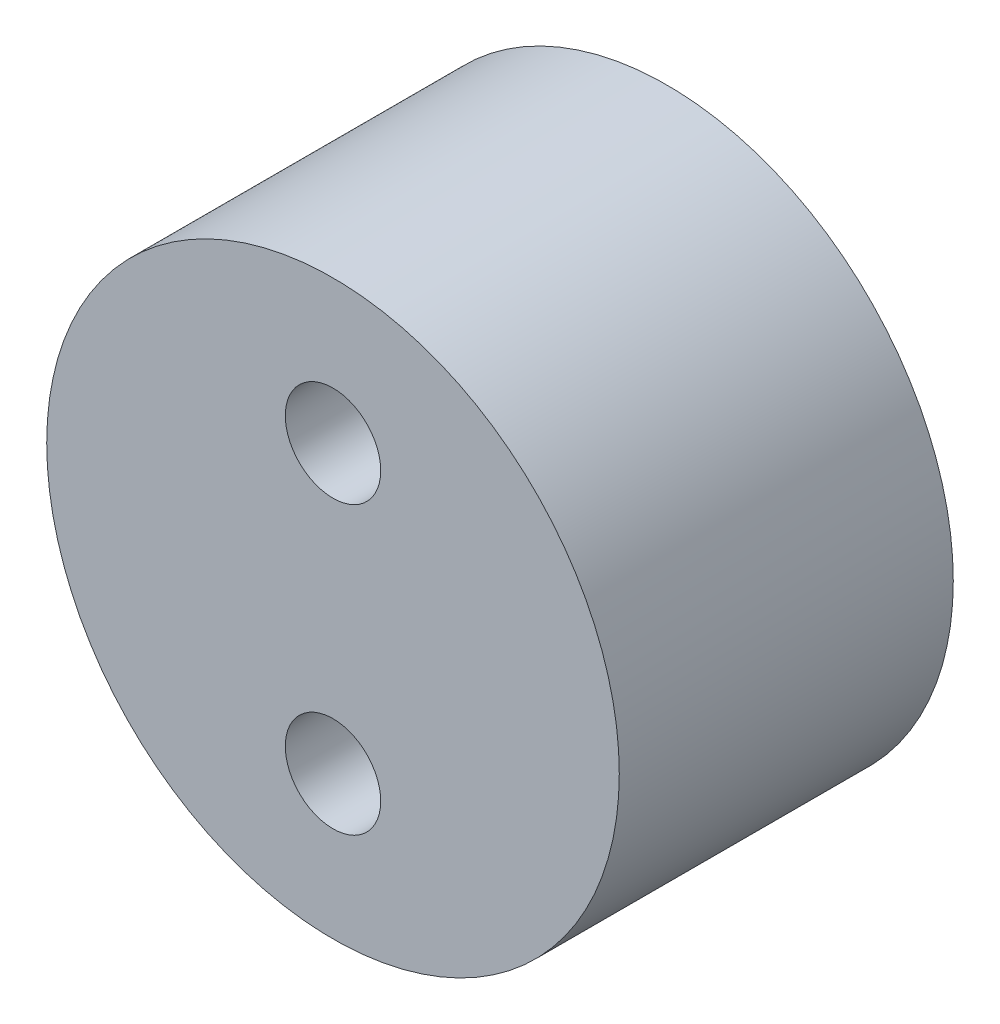
SolidWorks part; units mm, degrees
ref_plane "Front Plane" through (0, 0, 0) normal (0, 0, 1) x (1, 0, 0)
ref_plane "Top Plane" through (0, 0, 0) normal (0, 1, 0) x (1, 0, 0)
ref_plane "Right Plane" through (0, 0, 0) normal (1, 0, 0) x (0, 0, -1)
sketch "Sketch1" plane through (0, 0, 0) normal (0, 0, 1) x (1, 0, 0)
  line L0 (0, -7.5) -> (0, 7.5) construction
  circle A0 centre (0, 0) radius 15
  circle A1 centre (0, 7.5) radius 2.5
  circle A2 centre (0, -7.5) radius 2.5
  point P6 (0, 0)
  dimension "D2" = 30
  dimension "D3" = 5
  dimension "D4" = 5
  dimension "D1" = 15
extrude "Boss-Extrude1" add sketch "Sketch1" along normal blind 17.5
